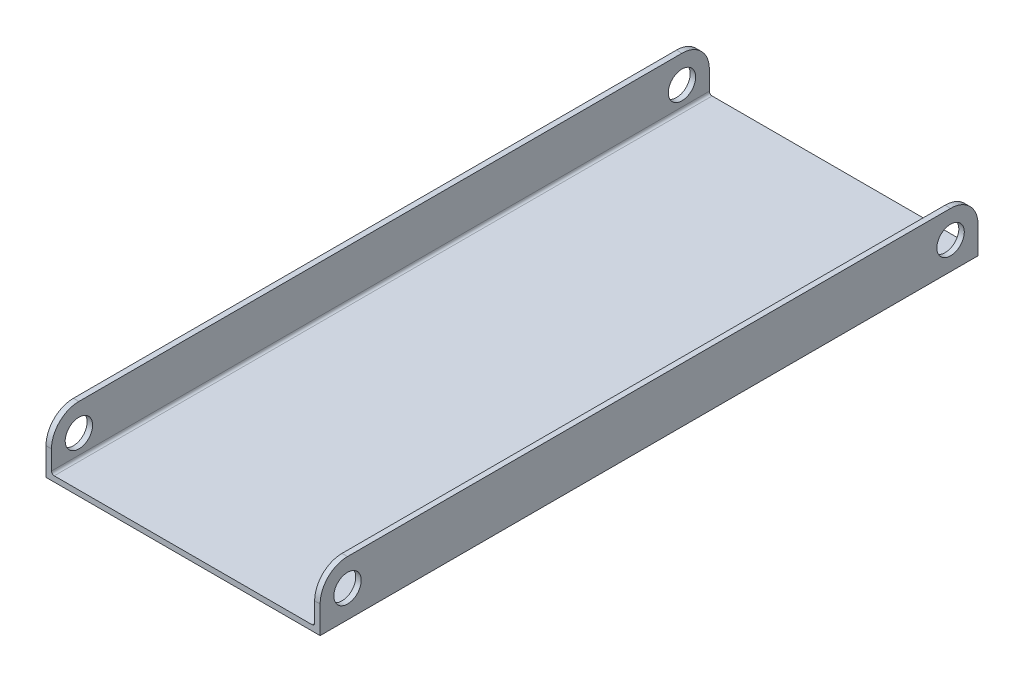
SolidWorks part; units mm, degrees
material "AISI 1020"
ref_plane "Front Plane" through (0, 0, 0) normal (0, 0, 1) x (1, 0, 0)
ref_plane "Top Plane" through (0, 0, 0) normal (0, 1, 0) x (1, 0, 0)
ref_plane "Right Plane" through (0, 0, 0) normal (1, 0, 0) x (0, 0, -1)
sketch "Sketch1" plane through (0, 0, 0) normal (0, 0, 1) x (1, 0, 0)
  line L0 (-30.48, 11.43) -> (-30.48, 0.635)
  line L1 (-29.845, 0) -> (29.845, 0)
  line L2 (30.48, 0.635) -> (30.48, 11.43)
  line L3 (-31.75, 11.43) -> (-31.75, -1.27)
  line L4 (-31.75, -1.27) -> (31.75, -1.27)
  line L5 (31.75, -1.27) -> (31.75, 11.43)
  line L6 (-30.48, 11.43) -> (-31.75, 11.43)
  line L7 (30.48, 11.43) -> (31.75, 11.43)
  line L8 (-30.48, 0) -> (30.48, 0) construction
  line L9 (30.48, 0) -> (30.48, 11.43) construction
  line L10 (-30.48, 11.43) -> (-30.48, 0) construction
  arc A0 (29.845, 0) -> (30.48, 0.635) centre (29.845, 0.635) ccw
  arc A1 (-30.48, 0.635) -> (-29.845, 0) centre (-29.845, 0.635) ccw
  point P2 (0, 0)
  point P6 (0, 0)
  dimension "D4" = 0.635
  dimension "D1" = 60.96
  dimension "D2" = 11.43
  dimension "D3" = 1.27
extrude "Boss-Extrude1" add sketch "Sketch1" against normal blind 152.4
fillet "Fillet1" radius 6.35 4 edges at (31.115, 11.43, -152.4) (-31.115, 11.43, -152.4) (31.115, 11.43, 0) (-31.115, 11.43, 0)
sketch "Sketch2" plane through (31.75, 0, 0) normal (1, 0, 0) x (0, 0, -1)
  line L0 (0, -1.27) -> (0, 5.08) construction
  line L1 (152.4, -1.27) -> (0, -1.27) construction
  line L2 (76.2, -1.27) -> (76.2, 11.43) construction
  line L3 (146.05, 11.43) -> (6.35, 11.43) construction
  circle A0 centre (6.35, 5.08) radius 3.175
  circle A1 centre (146.05, 5.08) radius 3.175
  dimension "D1" = 6.35
  dimension "D3" = 6.35
  dimension "D2" = 6.35
extrude "Cut-Extrude1" cut sketch "Sketch2" against normal through all
